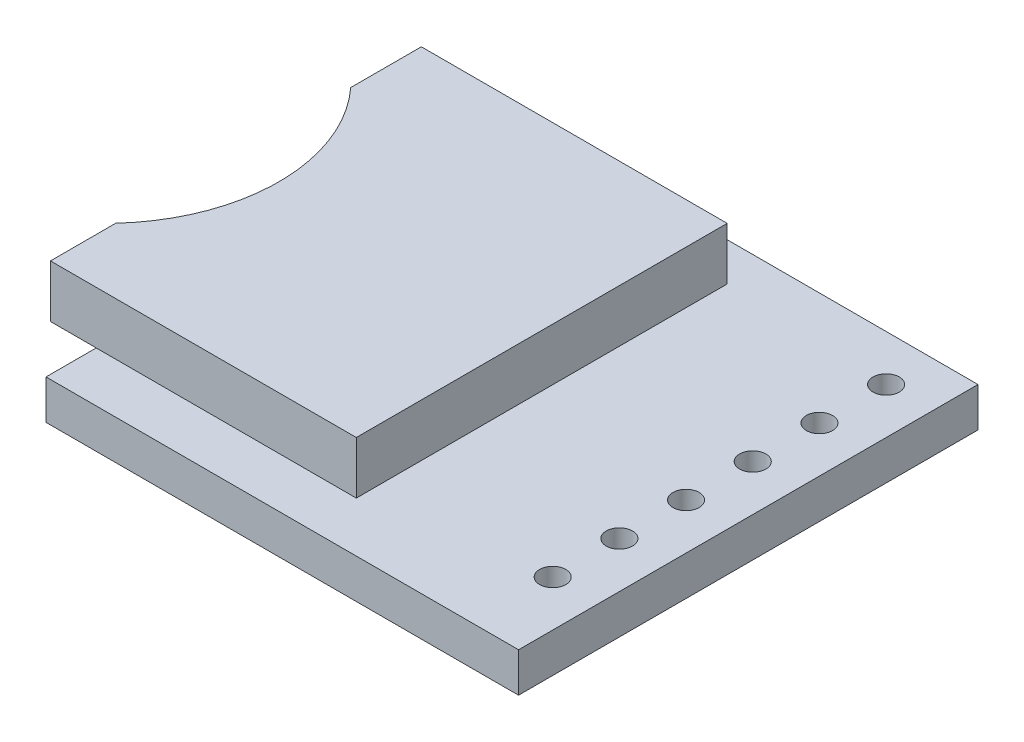
SolidWorks part; units mm, degrees
ref_plane "Front Plane" through (0, 0, 0) normal (0, 0, 1) x (1, 0, 0)
ref_plane "Top Plane" through (0, 0, 0) normal (0, 1, 0) x (1, 0, 0)
ref_plane "Right Plane" through (0, 0, 0) normal (1, 0, 0) x (0, 0, -1)
sketch "Sketch1" plane through (0, 0, 0) normal (0, 1, 0) x (1, 0, 0)
  line L0 (18.368, 53.0223) -> (98.4196, 53.0223) construction
  line L2 (18, 17.5) -> (0, 17.5)
  line L3 (18, 17.5) -> (18, 0)
  line L4 (18, 0) -> (0, 0)
  line L5 (0, 17.5) -> (0, 0)
  point P6 (0, 0)
  dimension "D1" = 17.5
  dimension "D2" = 18
extrude "Boss-Extrude1" add sketch "Sketch1" along normal blind 1.5
sketch "Sketch2" plane through (0, 1.5, 0) normal (0, 1, 0) x (1, 0, 0)
  line L0 (17.8827, 52.5) -> (97.216, 52.5) construction
  line L1 (-1.7424, 4.3971) -> (-1.7424, 1.9122)
  line L2 (9.9073, 16.0393) -> (-1.7424, 16.0393)
  line L3 (9.9073, 16.0393) -> (9.9073, 1.9122)
  line L4 (9.9073, 1.9122) -> (-1.7424, 1.9122)
  line L5 (-1.7424, 16.0393) -> (-1.7424, 13.3492)
  arc A0 (-1.7424, 13.3492) -> (-1.7424, 4.3971) centre (-6.6206, 8.8731) cw
extrude "Boss-Extrude2" add sketch "Sketch2" along normal blind 2
sketch "Sketch3" plane through (0, 1.5, 0) normal (0, 1, 0) x (1, 0, 0)
  line L0 (18, 17.5) -> (0, 17.5) construction
  line L1 (18, 0) -> (18, 17.5) construction
  circle A0 centre (16.25, 15.75) radius 0.5
  circle A1 centre (16.25, 13.21) radius 0.5
  circle A2 centre (16.25, 10.67) radius 0.5
  circle A3 centre (16.25, 8.13) radius 0.5
  circle A4 centre (16.25, 5.59) radius 0.5
  circle A5 centre (16.25, 3.05) radius 0.5
  dimension "D1" = 1
  dimension "D3" = 1.75
  dimension "D4" = 1.75
  dimension "D2" = 6
extrude "Cut-Extrude1" cut sketch "Sketch3" against normal through all
sketch "Sketch4" plane through (-1.7424, 0, 0) normal (-1, 0, 0) x (0, 0, 1)
  line L1 (-14.5045, 2.9892) -> (-3.0525, 2.9892)
  line L2 (-14.5045, 2.9892) -> (-14.5045, 2.0206)
  line L3 (-14.5045, 2.0206) -> (-3.0525, 2.0206)
  line L4 (-3.0525, 2.9892) -> (-3.0525, 2.0206)
extrude "Cut-Extrude2" cut sketch "Sketch4" against normal offset from surface (9.6496 mm away) 2 up to face at (9.9073, 2.5, -8.9758)
